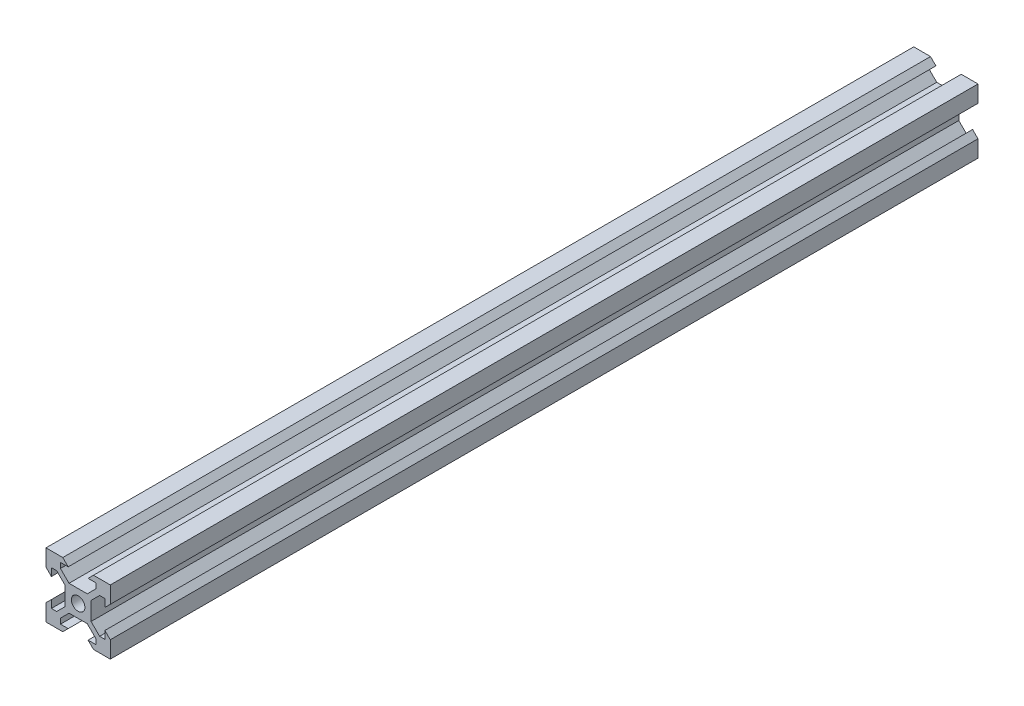
SolidWorks part; units mm, degrees
ref_plane "Front Plane" through (0, 0, 0) normal (0, 0, 1) x (1, 0, 0)
ref_plane "Top Plane" through (0, 0, 0) normal (0, 1, 0) x (1, 0, 0)
ref_plane "Right Plane" through (0, 0, 0) normal (1, 0, 0) x (0, 0, -1)
sketch "Sketch2" plane through (0, 0, 0) normal (0, 0, 1) x (1, 0, 0)
  line L0 (-4.775, 10) -> (-3.1, 8.325)
  line L1 (-10, 10) -> (-4.775, 10)
  line L2 (-10, 10) -> (-10, 4.775)
  line L3 (-10, -10) -> (-4.775, -10)
  line L4 (10, 10) -> (10, 4.775)
  line L5 (-5.5, 8.325) -> (-3.1, 8.325)
  line L6 (-5.5, 8.325) -> (-5.5, 6.685)
  line L7 (-2.84, 4.025) -> (2.84, 4.025)
  line L8 (5.5, 8.325) -> (5.5, 6.685)
  line L9 (-3.1, 8.325) -> (3.1, 8.325) construction
  line L10 (3.1, 8.325) -> (4.775, 10)
  line L11 (3.1, 8.325) -> (5.5, 8.325)
  line L12 (-5.5, 6.685) -> (-2.84, 4.025)
  line L13 (2.84, 4.025) -> (5.5, 6.685)
  line L14 (10, 4.775) -> (8.325, 3.1)
  line L15 (8.325, 5.5) -> (8.325, 3.1)
  line L16 (8.325, 5.5) -> (6.685, 5.5)
  line L17 (4.025, 2.84) -> (4.025, -2.84)
  line L18 (8.325, -5.5) -> (6.685, -5.5)
  line L19 (8.325, -3.1) -> (10, -4.775)
  line L20 (8.325, -3.1) -> (8.325, -5.5)
  line L21 (6.685, 5.5) -> (4.025, 2.84)
  line L22 (4.025, -2.84) -> (6.685, -5.5)
  line L23 (8.325, 3.1) -> (8.325, -3.1) construction
  line L24 (4.775, -10) -> (3.1, -8.325)
  line L25 (5.5, -8.325) -> (3.1, -8.325)
  line L26 (5.5, -8.325) -> (5.5, -6.685)
  line L27 (2.84, -4.025) -> (-2.84, -4.025)
  line L28 (-5.5, -8.325) -> (-5.5, -6.685)
  line L29 (-3.1, -8.325) -> (-4.775, -10)
  line L30 (-3.1, -8.325) -> (-5.5, -8.325)
  line L31 (5.5, -6.685) -> (2.84, -4.025)
  line L32 (-2.84, -4.025) -> (-5.5, -6.685)
  line L33 (3.1, -8.325) -> (-3.1, -8.325) construction
  line L34 (-10, -4.775) -> (-8.325, -3.1)
  line L35 (-8.325, -5.5) -> (-8.325, -3.1)
  line L36 (-8.325, -5.5) -> (-6.685, -5.5)
  line L37 (-4.025, -2.84) -> (-4.025, 2.84)
  line L38 (-8.325, 5.5) -> (-6.685, 5.5)
  line L39 (-8.325, 3.1) -> (-10, 4.775)
  line L40 (-8.325, 3.1) -> (-8.325, 5.5)
  line L41 (-6.685, -5.5) -> (-4.025, -2.84)
  line L42 (-4.025, 2.84) -> (-6.685, 5.5)
  line L43 (-8.325, -3.1) -> (-8.325, 3.1) construction
  line L44 (4.775, 10) -> (10, 10)
  line L45 (-10, -4.775) -> (-10, -10)
  line L46 (4.775, -10) -> (10, -10)
  line L47 (10, -4.775) -> (10, -10)
  circle A0 centre (0, 0) radius 2.1
  point P4 (-8.325, 0)
  point P8 (0, 4.025)
  point P15 (0, 8.325)
  point P52 (0, 0)
  dimension "D9" = 4.2
  dimension "D1" = 20
  dimension "D2" = 9.55
  dimension "D3" = 6.2
  dimension "D4" = 11
  dimension "D5" = 5.68
  dimension "D6" = 1.64
  dimension "D7" = 45
  dimension "D8" = 4
extrude "Boss-Extrude1" add sketch "Sketch2" along normal blind 270
